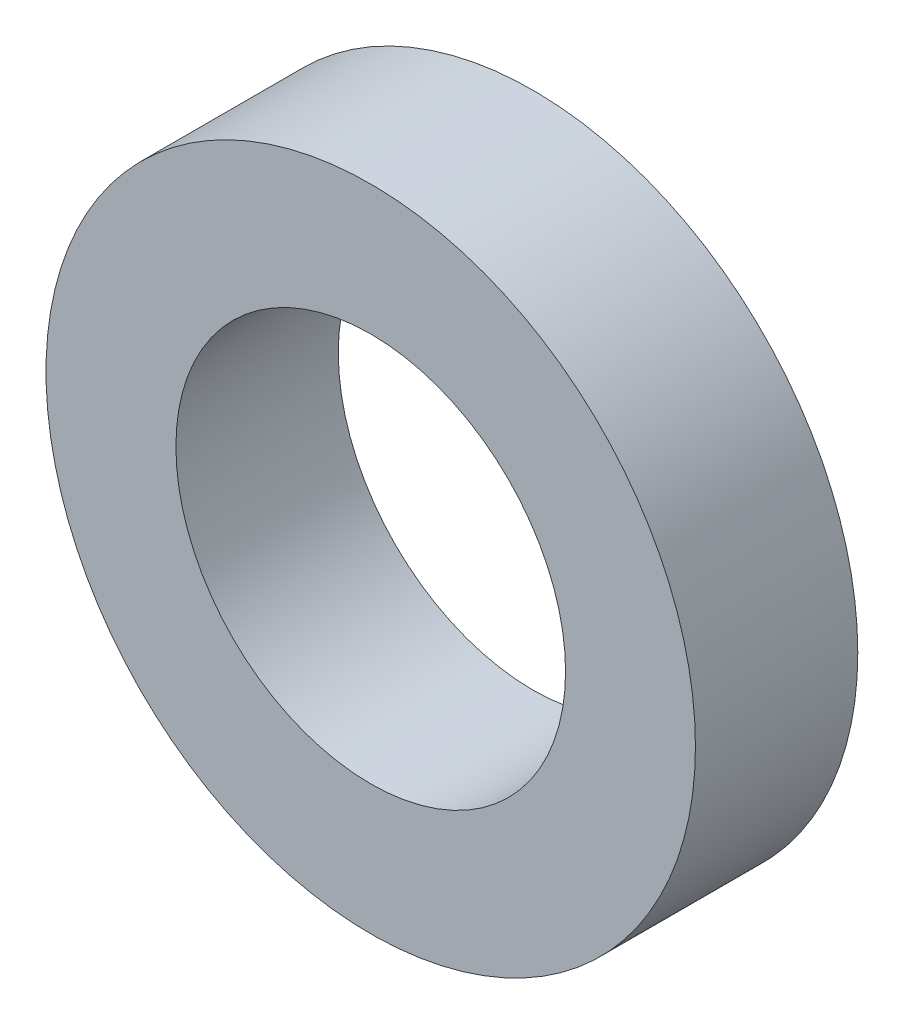
SolidWorks part; units mm, degrees
ref_plane "正面" through (0, 0, 0) normal (0, 0, 1) x (1, 0, 0)
ref_plane "平面" through (0, 0, 0) normal (0, 1, 0) x (1, 0, 0)
ref_plane "右側面" through (0, 0, 0) normal (1, 0, 0) x (0, 0, -1)
sketch "ｽｹｯﾁ1" plane through (0, 0, 0) normal (0, 0, 1) x (1, 0, 0)
  circle A0 centre (0, 0) radius 3
  circle A1 centre (0, 0) radius 5
  dimension "D1" = 6
  dimension "D2" = 10
extrude "ﾎﾞｽ - 押し出し1" add sketch "ｽｹｯﾁ1" along normal blind 2.5
